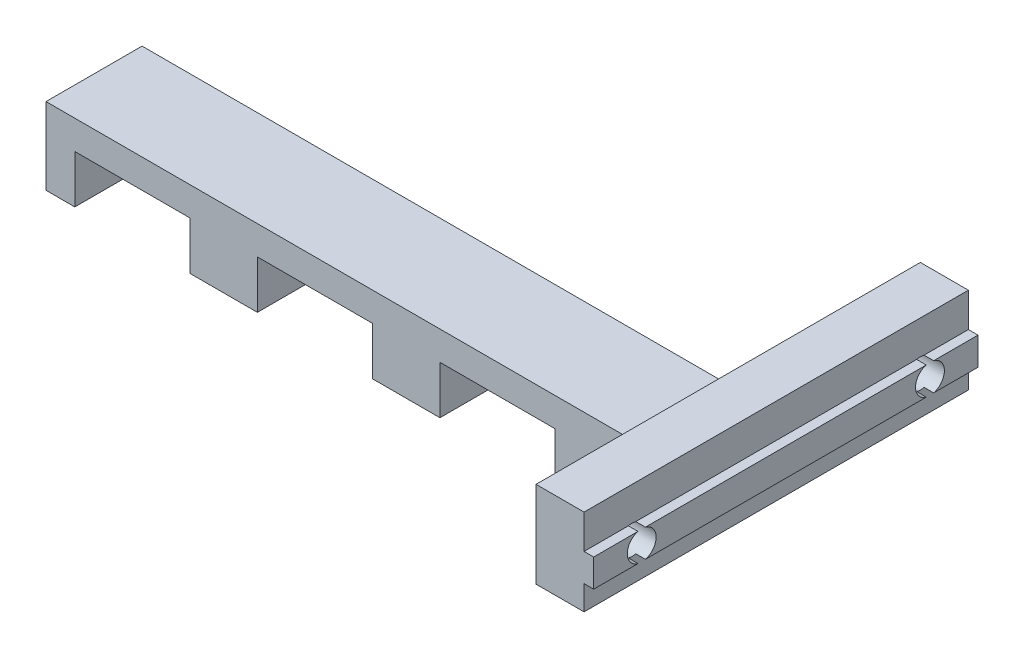
SolidWorks part; units mm, degrees
ref_plane "Front Plane" through (0, 0, 0) normal (0, 0, 1) x (1, 0, 0)
ref_plane "Top Plane" through (0, 0, 0) normal (0, 1, 0) x (1, 0, 0)
ref_plane "Right Plane" through (0, 0, 0) normal (1, 0, 0) x (0, 0, -1)
sketch "Esquisse1" plane through (0, 0, 0) normal (0, 0, 1) x (1, 0, 0)
  line L0 (3, 0) -> (3, 5)
  line L1 (3, 5) -> (15, 5)
  line L2 (15, 5) -> (15, 0)
  line L3 (15, 0) -> (22, 0)
  line L4 (22, 0) -> (22, 5)
  line L5 (22, 5) -> (34, 5)
  line L6 (34, 5) -> (34, 0)
  line L7 (34, 0) -> (41, 0)
  line L8 (41, 0) -> (41, 5)
  line L9 (41, 5) -> (53, 5)
  line L10 (53, 5) -> (53, 0)
  line L11 (53, 0) -> (60, 0)
  line L12 (71, 5) -> (71, 8)
  line L13 (71, 8) -> (0, 8)
  line L14 (0, 8) -> (0, 0)
  line L15 (0, 0) -> (3, 0)
  line L16 (60, 0) -> (60, 5)
  line L17 (60, 5) -> (71, 5)
  dimension "D2" = 12
  dimension "D3" = 12
  dimension "D4" = 12
  dimension "D5" = 3
  dimension "D6" = 11
  dimension "D7" = 8
  dimension "D8" = 3
  dimension "D9" = 7
  dimension "D10" = 7
  dimension "D11" = 7
extrude "Main" add sketch "Esquisse1" along normal mid plane 10
sketch "Sketch1" plane through (0, 0, 0) normal (0, 0, 1) x (1, 0, 0)
  line L0 (66, 14) -> (71, 14)
  line L2 (71, 14) -> (71, 10.45)
  line L4 (71, 10.45) -> (72, 10.45)
  line L5 (72, 10.45) -> (72, 7.55)
  line L6 (72, 7.55) -> (71, 7.55)
  line L7 (71, 7.55) -> (71, 5)
  line L8 (71, 5) -> (66, 5)
  line L10 (66, 5) -> (66, 14)
  line L11 (60, 5) -> (71, 5) construction
  dimension "D1" = 5
  dimension "D2" = 2.9
  dimension "D3" = 2.55
  dimension "D4" = 1
  dimension "D5" = 9
  dimension "D6" = 3.55
extrude "MakerBeamFix" add sketch "Sketch1" along normal mid plane 40
sketch "Sketch2" plane through (72, 0, 0) normal (1, 0, 0) x (0, 0, -1)
  line L0 (-20, 7.55) -> (-20, 10.45) construction
  line L1 (20, 7.55) -> (20, 10.45) construction
  circle A0 centre (-15, 9) radius 1.5
  circle A1 centre (15, 9) radius 1.5
  point P4 (-20, 9)
  dimension "D3" = 3
  dimension "D1" = 5
  dimension "D2" = 5
  dimension "D4" = 30
extrude "MakerBeamFixHole" cut sketch "Sketch2" against normal blind 30
fillet "Fillet1" radius 5 3 edges at (66, 6.5, -5) (66, 6.5, 5) (66, 8, 0)
